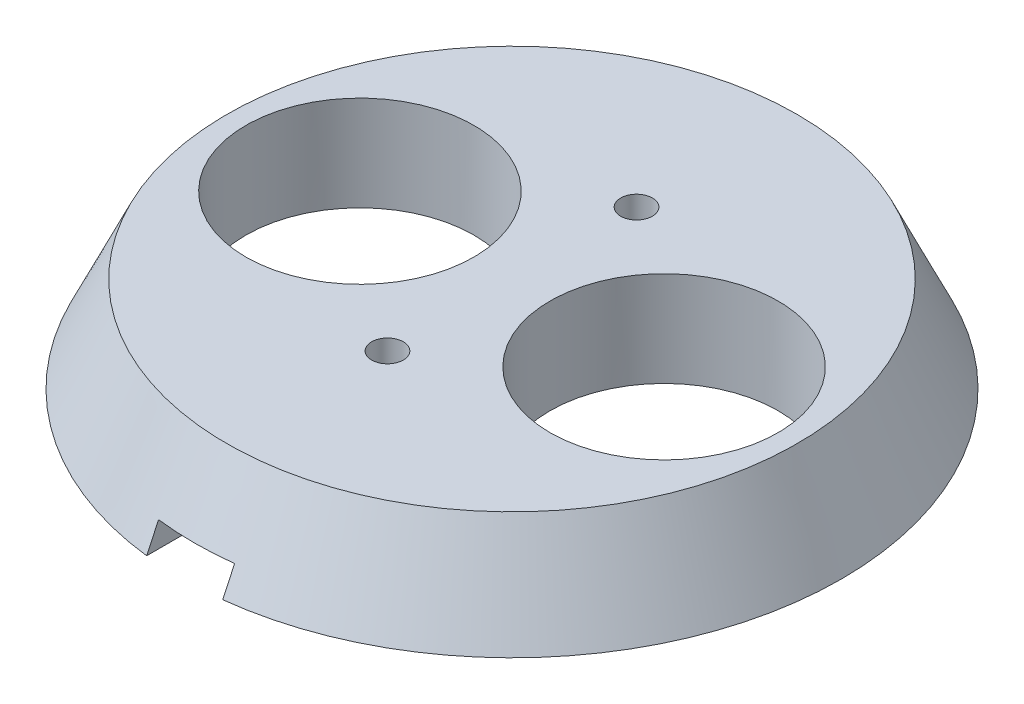
SolidWorks part; units mm, degrees
ref_plane "Front Plane" through (0, 0, 0) normal (0, 0, 1) x (1, 0, 0)
ref_plane "Top Plane" through (0, 0, 0) normal (0, 1, 0) x (1, 0, 0)
ref_plane "Right Plane" through (0, 0, 0) normal (1, 0, 0) x (0, 0, -1)
sketch "Sketch1" plane through (0, 0, 0) normal (0, 1, 0) x (1, 0, 0)
  line L1 (-103.5, 53) -> (103.5, 53)
  line L2 (-103.5, 53) -> (-103.5, -53)
  line L3 (-103.5, -53) -> (103.5, -53)
  line L4 (103.5, 53) -> (103.5, -53)
  line L5 (-103.5, 53) -> (103.5, -53) construction
  line L6 (-103.5, -53) -> (103.5, 53) construction
  point P0 (0, 0)
  dimension "D1" = 207
  dimension "D2" = 106
extrude "Boss-Extrude1" add sketch "Sketch1" along normal blind 35.5
sketch "Sketch2" plane through (0, 35.5, 0) normal (0, 1, 0) x (1, 0, 0)
  line L0 (103.5, 53) -> (-103.5, 53) construction
  line L1 (-100.5, 50) -> (100.5, 50)
  line L2 (-100.5, 50) -> (-100.5, -50)
  line L3 (-100.5, -50) -> (100.5, -50)
  line L4 (100.5, 50) -> (100.5, -50)
  line L5 (-100.5, 50) -> (100.5, -50) construction
  line L6 (-100.5, -50) -> (100.5, 50) construction
  line L7 (-103.5, 53) -> (-103.5, -53) construction
  point P0 (0, 0)
  dimension "D1" = 3
  dimension "D2" = 3
extrude "Cut-Extrude1" cut sketch "Sketch2" against normal blind 32
sketch "Sketch3" plane through (0, 35.5, 0) normal (0, 1, 0) x (1, 0, 0)
  line L0 (-103.5, -53) -> (103.5, -53) construction
  line L1 (-102, 51.5) -> (102, 51.5)
  line L2 (-102, 51.5) -> (-102, -51.5)
  line L3 (-102, -51.5) -> (102, -51.5)
  line L4 (102, 51.5) -> (102, -51.5)
  line L5 (-100.5, 50) -> (100.5, 50)
  line L6 (-100.5, 50) -> (-100.5, -50)
  line L7 (-100.5, -50) -> (100.5, -50)
  line L8 (100.5, 50) -> (100.5, -50)
  dimension "D1" = 1.5
  dimension "D2" = 1.5
  dimension "D3" = 1.5
  dimension "D4" = 1.5
extrude "Cut-Extrude2" cut sketch "Sketch3" against normal blind 3
hole_wizard "M18 Clearance Hole2" positions "3DSketch2" profile "Sketch5" hole size "M18" standard "ANSI Metric" end condition through all
sketch3d "3DSketch2"
  line L0 (100.5, 3.5, -50) -> (-100.5, 3.5, -50) construction
  line L1 (100.5, 3.5, 50) -> (100.5, 3.5, -50) construction
  point P0 (64.5, 3.5, 5)
  point P2 (40.5, 3.5, 5)
  dimension "D1" = 55
  dimension "D2" = 55
  dimension "D3" = 36
  dimension "D4" = 24
sketch "Sketch5" plane through (64.5, 3.5, 5) normal (1, 0, 0) x (0, 0, 1)
  line L0 (0, 0) -> (0, 3.5)
  line L1 (0, 3.5) -> (9, 3.5)
  line L2 (9, 3.5) -> (9, 0)
  line L5 (9, 0) -> (0, 0)
  line L11 (0, -6.35) -> (0, 107.95) construction
  dimension "Thru Hole Dia." = 18
  dimension "Thru Hole Depth" = 3.5
fillet "Fillet1" radius 2 12 edges at (103.5, 0, 0) (0, 0, -53) (-103.5, 0, 0) (0, 0, 53) (100.5, 18, -50) (100.5, 18, 50) (-100.5, 18, 50) (-100.5, 18, -50) (-103.5, 17.75, -53) (103.5, 17.75, -53) (103.5, 17.75, 53) (-103.5, 17.75, 53)
fillet "Fillet2" radius 2 4 edges at (-102, 34, -51.5) (-102, 34, 51.5) (102, 34, 51.5) (102, 34, -51.5)
sketch "Sketch6" plane through (0, 3.5, 0) normal (0, 1, 0) x (1, 0, 0)
  line L0 (98.5, 50) -> (-98.5, 50) construction
  line L1 (-48.5, 50) -> (-38.5, 50)
  line L2 (-48.5, 50) -> (-48.5, 40)
  line L3 (-48.5, 40) -> (-38.5, 40)
  line L4 (-38.5, 50) -> (-38.5, 40)
  line L5 (100.5, -48) -> (100.5, 48) construction
  dimension "D1" = 10
  dimension "D2" = 10
  dimension "D3" = 139
extrude "Boss-Extrude2" add sketch "Sketch6" along normal blind 29
sketch "Sketch7" plane through (0, 3.5, 0) normal (0, 1, 0) x (1, 0, 0)
  line L0 (-98.5, -50) -> (98.5, -50) construction
  line L1 (-48.5, -50) -> (-38.5, -50)
  line L2 (-48.5, -50) -> (-48.5, -40)
  line L3 (-48.5, -40) -> (-38.5, -40)
  line L4 (-38.5, -50) -> (-38.5, -40)
  line L5 (100.5, -48) -> (100.5, 48) construction
  dimension "D1" = 10
  dimension "D2" = 10
  dimension "D3" = 139
extrude "Boss-Extrude3" add sketch "Sketch7" along normal blind 29
sketch "Sketch8" plane through (0, 3.5, 0) normal (0, 1, 0) x (1, 0, 0)
  line L0 (100.5, -48) -> (100.5, 48) construction
  line L1 (100.5, 25) -> (90.5, 25)
  line L2 (100.5, 25) -> (100.5, 15)
  line L3 (100.5, 15) -> (90.5, 15)
  line L4 (90.5, 25) -> (90.5, 15)
  line L5 (98.5, 50) -> (-38.5, 50) construction
  dimension "D1" = 10
  dimension "D2" = 10
  dimension "D3" = 25
extrude "Boss-Extrude4" add sketch "Sketch8" along normal blind 29
sketch "Sketch9" plane through (0, 3.5, 0) normal (0, 1, 0) x (1, 0, 0)
  line L0 (100.5, -48) -> (100.5, 15) construction
  line L1 (100.5, -15) -> (90.5, -15)
  line L2 (100.5, -15) -> (100.5, -25)
  line L3 (100.5, -25) -> (90.5, -25)
  line L4 (90.5, -15) -> (90.5, -25)
  line L5 (-38.5, -50) -> (98.5, -50) construction
  dimension "D1" = 10
  dimension "D2" = 10
  dimension "D3" = 25
extrude "Boss-Extrude5" add sketch "Sketch9" along normal blind 29
hole_wizard "M3 Clearance Hole1" positions "3DSketch4" profile "Sketch11" hole size "M3" standard "ANSI Metric"
sketch3d "3DSketch4"
  line L0 (-48.5, 32.5, -40) -> (-38.5, 32.5, -40) construction
  line L1 (-38.5, 32.5, -40) -> (-38.5, 32.5, -50) construction
  line L2 (-38.5, 32.5, 40) -> (-48.5, 32.5, 40) construction
  line L3 (-38.5, 32.5, 50) -> (-38.5, 32.5, 40) construction
  line L4 (90.5, 32.5, -25) -> (90.5, 32.5, -15) construction
  line L5 (100.5, 32.5, -25) -> (90.5, 32.5, -25) construction
  line L6 (90.5, 32.5, 15) -> (90.5, 32.5, 25) construction
  line L7 (100.5, 32.5, 15) -> (90.5, 32.5, 15) construction
  point P0 (-43.5, 32.5, -45)
  point P2 (-43.5, 32.5, 45)
  point P4 (95.5, 32.5, 20)
  point P6 (95.5, 32.5, -20)
  dimension "D1" = 5
  dimension "D2" = 5
  dimension "D3" = 5
  dimension "D4" = 5
  dimension "D5" = 5
  dimension "D6" = 5
  dimension "D7" = 5
  dimension "D8" = 5
sketch "Sketch11" plane through (-43.5, 32.5, -45) normal (1, 0, 0) x (0, 0, 1)
  line L0 (0, 0) -> (0, 27.0215)
  line L1 (0, 27.0215) -> (1.7, 26)
  line L2 (1.7, 26) -> (1.7, 0)
  line L5 (1.7, 0) -> (0, 0)
  line L10 (0, 27.0215) -> (-1.7, 26) construction
  line L11 (0, -6.35) -> (0, 107.95) construction
  dimension "Hole Dia." = 3.4
  dimension "Hole Depth" = 26
  dimension "Drill Angle" = 118
sketch "Sketch12" plane through (0, 0, 0) normal (0, -1, 0) x (1, 0, 0)
  line L0 (-38.5, 50) -> (-38.5, 40) construction
  line L1 (-38.5, 40) -> (-48.5, 40) construction
  circle A0 centre (-43.5, 45) radius 3
  dimension "D1" = 5
  dimension "D2" = 5
extrude "Cut-Extrude4" cut sketch "Sketch12" against normal blind 6
sketch "Sketch13" plane through (0, 0, 0) normal (0, -1, 0) x (1, 0, 0)
  line L0 (-38.5, -40) -> (-38.5, -50) construction
  line L1 (-48.5, -40) -> (-38.5, -40) construction
  circle A0 centre (-43.5, -45) radius 3
  dimension "D1" = 5
  dimension "D2" = 5
extrude "Cut-Extrude5" cut sketch "Sketch13" against normal blind 6
sketch "Sketch14" plane through (0, 0, 0) normal (0, -1, 0) x (1, 0, 0)
  line L0 (100.5, 48) -> (100.5, 25) construction
  line L1 (100.5, 15) -> (90.5, 15) construction
  circle A0 centre (95.5, 20) radius 3
  dimension "D1" = 5
  dimension "D2" = 5
extrude "Cut-Extrude6" cut sketch "Sketch14" against normal blind 6
sketch "Sketch15" plane through (0, 0, 0) normal (0, -1, 0) x (1, 0, 0)
  line L0 (90.5, -15) -> (100.5, -15) construction
  line L1 (90.5, -25) -> (90.5, -15) construction
  circle A0 centre (95.5, -20) radius 3
  dimension "D1" = 5
  dimension "D2" = 5
extrude "Cut-Extrude8" cut sketch "Sketch15" against normal blind 6
ref_plane "Plane3" through (0, -7.5, 0) normal (0, 1, 0) x (1, 0, 0)
sketch "Sketch16" plane through (0, -7.5, 0) normal (0, 1, 0) x (1, 0, 0)
  line L0 (100.5, -15) -> (100.5, 15) construction
  line L1 (98.5, 50) -> (-38.5, 50) construction
  circle A0 centre (52.5, -5) radius 26
  dimension "D1" = 48
  dimension "D2" = 55
sketch "Sketch17" plane through (0, 0, 0) normal (0, 1, 0) x (1, 0, 0)
  circle A0 centre (52.5, -5) radius 22.5
loft "Loft2" add profiles "Sketch17", "Sketch16"
sketch "Sketch18" plane through (0, -7.5, 0) normal (0, -1, 0) x (1, 0, 0)
  line L0 (100.5, 15) -> (100.5, -15) construction
  line L1 (98.5, -50) -> (-38.5, -50) construction
  circle A0 centre (40.5, 5) radius 9
  dimension "D1" = 60
  dimension "D2" = 55
extrude "Cut-Extrude9" cut sketch "Sketch18" against normal through all
sketch "Sketch19" plane through (0, -7.5, 0) normal (0, -1, 0) x (1, 0, 0)
  line L0 (100.5, 15) -> (100.5, -15) construction
  line L1 (98.5, -50) -> (-38.5, -50) construction
  circle A0 centre (64.5, 5) radius 9
  dimension "D1" = 36
  dimension "D2" = 55
extrude "Cut-Extrude10" cut sketch "Sketch19" against normal through all
sketch "Sketch20" plane through (0, -7.5, 0) normal (0, -1, 0) x (1, 0, 0)
  line L0 (100.5, 15) -> (100.5, -15) construction
  line L1 (49.5, 19.8263) -> (55.5, 19.8263)
  line L2 (49.5, 19.8263) -> (49.5, 30.8263)
  line L3 (49.5, 30.8263) -> (55.5, 30.8263)
  line L4 (55.5, 19.8263) -> (55.5, 30.8263)
  line L5 (49.5, 19.8263) -> (55.5, 30.8263) construction
  line L6 (49.5, 30.8263) -> (55.5, 19.8263) construction
  circle A0 centre (52.5, 5) radius 26 construction
  point P0 (52.5, 25.3263)
  dimension "D1" = 48
  dimension "D2" = 6
  dimension "D3" = 11
extrude "Cut-Extrude13" cut sketch "Sketch20" against normal blind 2
sketch "Sketch21" plane through (0, -7.5, 0) normal (0, -1, 0) x (1, 0, 0)
  line L0 (100.5, 15) -> (100.5, -15) construction
  line L1 (49.5, -9.8263) -> (55.5, -9.8263)
  line L2 (49.5, -9.8263) -> (49.5, -20.8263)
  line L3 (49.5, -20.8263) -> (55.5, -20.8263)
  line L4 (55.5, -9.8263) -> (55.5, -20.8263)
  line L5 (49.5, -9.8263) -> (55.5, -20.8263) construction
  line L6 (49.5, -20.8263) -> (55.5, -9.8263) construction
  arc A0 (49.5, 30.8263) -> (55.5, 30.8263) centre (52.5, 5) ccw construction
  point P0 (52.5, -15.3263)
  dimension "D1" = 48
  dimension "D2" = 11
  dimension "D3" = 6
extrude "Cut-Extrude14" cut sketch "Sketch21" against normal blind 2
sketch "Sketch22" plane through (0, 0, 0) normal (0, -1, 0) x (1, 0, 0)
  line L1 (-107.166, 58.1169) -> (111.2877, 58.1169)
  line L2 (-107.166, 58.1169) -> (-107.166, -60.59)
  line L3 (-107.166, -60.59) -> (111.2877, -60.59)
  line L4 (111.2877, 58.1169) -> (111.2877, -60.59)
  circle A0 centre (52.5, 5) radius 34.6814
extrude "Cut-Extrude15" cut sketch "Sketch22" against normal through all
sketch "Sketch23" plane through (0, 3.5, 0) normal (0, 1, 0) x (1, 0, 0)
  circle A0 centre (52.5, -5) radius 34.6814
extrude "Cut-Extrude16" cut sketch "Sketch23" along normal blind 9 and the other way blind 3.5
hole_wizard "M3x0.5 Tapped Hole1" positions "3DSketch6" profile "Sketch25" tap size "M3x0.5" standard "ANSI Metric" end condition through all
sketch3d "3DSketch6"
  line L0 (49.5, -7.5, 30.8263) -> (49.5, -7.5, 19.8263) construction
  line L1 (49.5, -7.5, 19.8263) -> (55.5, -7.5, 19.8263) construction
  line L2 (49.5, -7.5, -9.8263) -> (49.5, -7.5, -20.8263) construction
  line L3 (55.5, -7.5, -9.8263) -> (49.5, -7.5, -9.8263) construction
  line L4 (55.5, -7.5, 19.8263) -> (55.5, -7.5, 30.8263) construction
  point P0 (52.5, -7.5, 14.8263)
  point P2 (52.5, -7.5, -4.8263)
  dimension "D1" = 3
  dimension "D2" = 5
  dimension "D3" = 3
  dimension "D4" = 5
  dimension "D5" = 3
sketch "Sketch25" plane through (52.5, -7.5, 14.8263) normal (1, 0, 0) x (0, 0, -1)
  line L0 (0, 0) -> (0, 7.5001)
  line L1 (0, 7.5001) -> (1.25, 7.5001)
  line L2 (1.25, 7.5001) -> (1.25, 0)
  line L5 (1.25, 0) -> (0, 0)
  line L11 (0, -6.35) -> (0, 107.95) construction
  dimension "Thread Major Dia." = 2.5
  dimension "Thru Tap Drill Depth" = 7.5001
